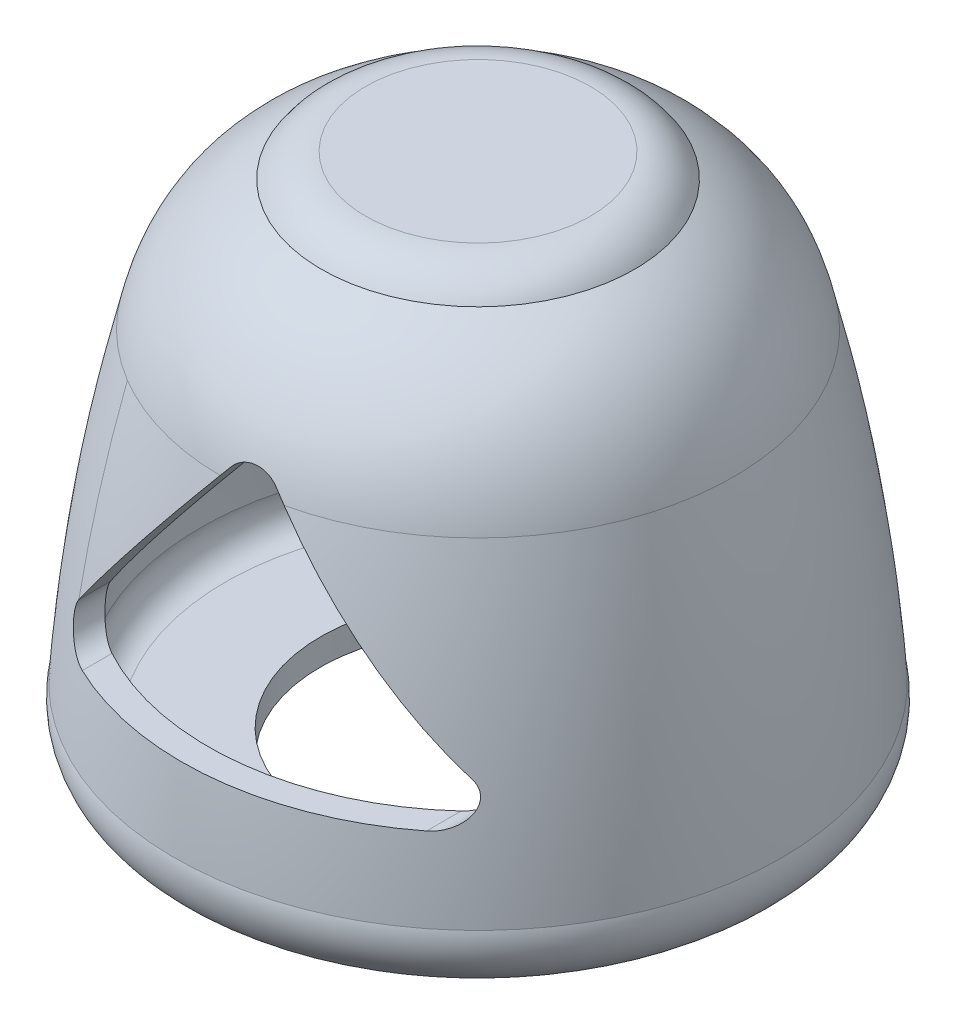
SolidWorks part; units mm, degrees
ref_plane "Front Plane" through (0, 0, 0) normal (0, 0, 1) x (1, 0, 0)
ref_plane "Top Plane" through (0, 0, 0) normal (0, 1, 0) x (1, 0, 0)
ref_plane "Right Plane" through (0, 0, 0) normal (1, 0, 0) x (0, 0, -1)
sketch "Sketch1" plane through (0, 0, 0) normal (0, 0, 1) x (1, 0, 0)
  line L0 (-60, -20) -> (-96.1257, -20)
  line L1 (0, 180) -> (-42.7924, 180)
  line L2 (-60, -10) -> (-96.1257, -10)
  line L3 (0, 170) -> (0, 180)
  line L4 (-60, -10) -> (-60, -20)
  line L5 (0, 170) -> (-42.7924, 170)
  arc A0 (-96.1257, -10) -> (-105.6126, 3.1623) centre (-96.1257, 0) cw
  arc A1 (-96.1257, -20) -> (-115.5203, 4.8837) centre (-96.1257, 0) cw
  arc A2 (-59.5807, 170.8699) -> (-42.7924, 180) centre (-42.7924, 160) cw
  arc A3 (-52.2792, 163.1623) -> (-42.7924, 170) centre (-42.7924, 160) cw
  spline S0 degree 2 poles (-105.6126, 3.1623) (-101.7617, 61.8869) (-87.5624, 119.1201) knots 0 0 0 1 1 1
  spline S1 degree 2 poles (-87.5624, 119.1201) (-80.6856, 151.4743) (-52.2792, 163.1623) knots 0 0 0 1 1 1
  spline S2 degree 1 poles (-115.5203, 4.8837) (-97.3078, 121.3681) knots 0 0 1 1 construction
  spline S3 degree 1 poles (-97.3078, 121.3681) (-59.5807, 170.8699) knots 0 0 1 1 construction
  spline S4 degree 3 poles (-115.5203, 4.8837) (-114.861, 14.7001) (-113.1105, 34.3188) (-109.2, 63.5295) (-104.0059, 92.5509) (-99.6781, 111.8041) (-97.3078, 121.3681) knots 0.008952 0.008952 0.008952 0.008952 0.256369 0.503787 0.751205 0.998623 0.998623 0.998623 0.998623
  spline S5 degree 3 poles (-97.3078, 121.3681) (-97.0068, 122.7717) (-96.3367, 125.5838) (-94.7693, 130.9935) (-92.3531, 137.4542) (-88.7087, 144.6602) (-84.3091, 151.2828) (-79.166, 157.2669) (-73.314, 162.5641) (-67.8827, 166.3803) (-63.2402, 169.0648) (-60.8077, 170.2923) (-59.5807, 170.8699) knots 0.002342 0.002342 0.002342 0.002342 0.061278 0.120214 0.238086 0.355958 0.47383 0.591702 0.709574 0.827446 0.886382 0.945317 0.945317 0.945317 0.945317
  point P20 (-50, 170)
  dimension "D1" = 10
  dimension "D4" = 10
  dimension "D6" = 50
revolve "Revolve1" add sketch "Sketch1" angle 360 about L3
ref_plane "Plane1" through (0, 0, 120) normal (0, 0, 1) x (1, 0, 0)
sketch "Sketch2" plane through (0, 0, 120) normal (0, 0, 1) x (1, 0, 0)
  line L0 (69.3523, 35.1464) -> (-49.0352, 35.1464)
  line L1 (-56.8438, 51.3933) -> (2.3499, 125.3855)
  line L2 (17.9673, 125.3855) -> (77.161, 51.3933)
  arc A0 (69.3523, 35.1464) -> (77.161, 51.3933) centre (69.3523, 45.1464) ccw
  arc A1 (17.9673, 125.3855) -> (2.3499, 125.3855) centre (10.1586, 119.1386) ccw
  arc A2 (-56.8438, 51.3933) -> (-49.0352, 35.1464) centre (-49.0352, 45.1464) ccw
  point P3 (10.1586, 35.1464)
  point P4 (10.1586, 35.1464)
  dimension "D1" = 10
extrude "Cut-Extrude1" cut sketch "Sketch2" against normal blind 90
